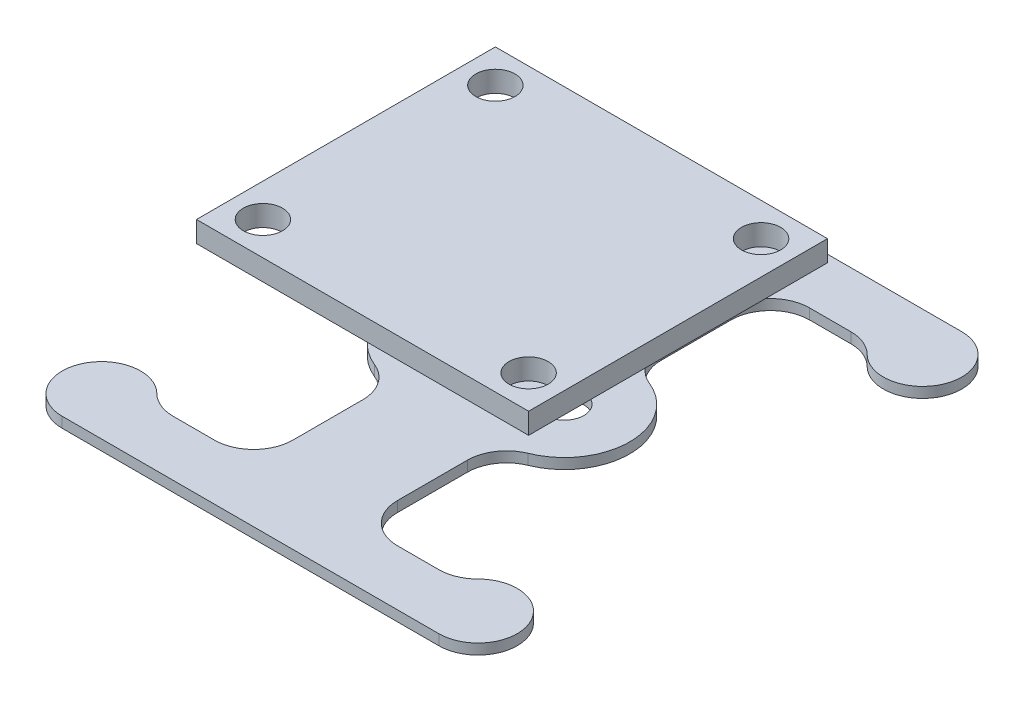
SolidWorks part; units mm, degrees
other "PCB" parameters "D1"=2.5369, "D2"=3.8414, "D7"=2.4726, "D8"=4.6276, "D9"=2.9996, "D3"=14.7024, "D4"=7.7197, "D5"=9.1404, "D6"=29.1565, "D10"=2.8284
ref_plane "Front Plane" through (0, 0, 0) normal (0, 0, 1) x (1, 0, 0)
ref_plane "Top Plane" through (0, 0, 0) normal (0, 1, 0) x (1, 0, 0)
ref_plane "Right Plane" through (0, 0, 0) normal (1, 0, 0) x (0, 0, -1)
sketch "Sketch1" plane through (0, 0, 0) normal (0, 1, 0) x (1, 0, 0)
  line L1 (-12.7, -11.43) -> (12.7, -11.43)
  line L2 (-12.7, -11.43) -> (-12.7, 11.43)
  line L3 (-12.7, 11.43) -> (12.7, 11.43)
  line L4 (12.7, -11.43) -> (12.7, 11.43)
  line L5 (0, 11.43) -> (0, -11.43) construction
  line L6 (-12.7, 0) -> (12.7, 0) construction
  line L7 (10.16, -8.89) -> (-10.16, -8.89) construction
  line L8 (10.16, -8.89) -> (10.16, 8.89) construction
  line L9 (10.16, 8.89) -> (-10.16, 8.89) construction
  line L10 (-10.16, -8.89) -> (-10.16, 8.89) construction
  line L11 (0, 8.89) -> (0, -8.89) construction
  line L12 (10.16, 0) -> (-10.16, 0) construction
  circle A0 centre (-10.16, 8.89) radius 1.5
  circle A1 centre (10.16, 8.89) radius 1.5
  circle A2 centre (10.16, -8.89) radius 1.5
  circle A3 centre (-10.16, -8.89) radius 1.5
  point P0 (0, 0)
  point P4 (0, 0)
  point P12 (0, 0)
  point P13 (0, 0)
  point P14 (0, 0)
  point P15 (0, 0)
  point P16 (0, 0)
  dimension "D5" = 3
  dimension "D1" = 22.86
  dimension "D2" = 25.4
  dimension "D3" = 17.78
  dimension "D4" = 20.32
extrude "Boss-Extrude1" add sketch "Sketch1" along normal blind 1.6
sketch "Sketch2" [suppressed] plane through (0, 0, 0) normal (0, -1, 0) x (1, 0, 0)
  line L0 (-12.7, 11.43) -> (12.7, 11.43) construction
  line L1 (-12.7, -11.43) -> (12.7, -11.43) construction
  line L4 (12.7, 11.43) -> (12.7, -11.43) construction
  line L5 (13.7441, -5.6224) -> (12.8573, -6.4309) construction
  line L6 (6.8924, 12.4741) -> (7.7009, 11.5873) construction
  circle A0 centre (-10.16, 8.89) radius 1.25
  circle A1 centre (-10.16, -8.89) radius 1.25
  circle A2 centre (10.16, -8.89) radius 1.25
  circle A3 centre (10.16, 8.89) radius 1.25
  circle A4 centre (-10.16, 8.89) radius 3.65
  circle A5 centre (-10.16, -8.89) radius 3.65
  circle A6 centre (10.16, -8.89) radius 3.65
  circle A7 centre (10.16, 8.89) radius 3.65
  circle A8 centre (4.1975, 15.43) radius 4
  circle A9 centre (4.1975, 15.43) radius 1.8
  circle A12 centre (16.7, -2.9275) radius 4
  circle A13 centre (16.7, -2.9275) radius 1.8
  circle A16 centre (-4.1975, -15.43) radius 1.8
  circle A17 centre (-4.1975, -15.43) radius 4
  circle A18 centre (-16.7, 2.9275) radius 4
  circle A19 centre (-16.7, 2.9275) radius 1.8
  point P25 (17.3377, -1.52)
  point P28 (-3.6878, -23.8739)
  point P29 (0, 0)
  point P33 (1.6609, -15.6434)
  point P36 (-3.0642, -15.43)
  point P43 (-3.5498, -5.6007)
  point P52 (0, 0)
  dimension "D1" = 2.5
  dimension "D3" = 8
  dimension "D4" = 3.6
  dimension "D5" = 1.2
  dimension "D2" = 2.4
  dimension "D6" = 2
extrude "Boss-Extrude2" [suppressed] add sketch "Sketch2" along normal blind 10 separate body
sketch "Sketch3" [suppressed] plane through (0, -10, 0) normal (0, -1, 0) x (1, 0, 0)
  line L0 (-10.16, 12.54) -> (-10.16, 13.74) construction
  line L1 (-20.7, -19.43) -> (20.7, -19.43)
  line L2 (-20.7, -19.43) -> (-20.7, 19.43)
  line L3 (-20.7, 19.43) -> (20.7, 19.43)
  line L4 (20.7, -19.43) -> (20.7, 19.43)
  line L5 (0, 19.43) -> (0, -19.43) construction
  line L6 (-20.7, 0) -> (20.7, 0) construction
  line L7 (15.01, -13.74) -> (-15.01, -13.74)
  line L8 (15.01, -13.74) -> (15.01, 13.74)
  line L9 (15.01, 13.74) -> (-15.01, 13.74)
  line L10 (-15.01, -13.74) -> (-15.01, 13.74)
  line L11 (0, 13.74) -> (0, -13.74) construction
  line L12 (15.01, 0) -> (-15.01, 0) construction
  line L13 (-13.81, 8.89) -> (-15.01, 8.89) construction
  circle A0 centre (4.1975, 15.43) radius 4 construction
  circle A1 centre (-16.7, 2.9275) radius 4 construction
  circle A2 centre (-10.16, 8.89) radius 3.65 construction
  point P0 (0, 0)
  point P8 (0, 0)
  point P12 (-10.16, 12.54)
  point P13 (-13.81, 8.89)
  point P20 (-16.2622, 15.2267)
  dimension "D1" = 1.2
extrude "Boss-Extrude3" [suppressed] add sketch "Sketch3" against normal up to surface (10 mm away)
sketch "Sketch4" [suppressed] plane through (0, 0, 0) normal (0, 1, 0) x (1, 0, 0)
  circle A0 centre (-16.7, -2.9275) radius 1.8 construction
  circle A1 centre (-4.1975, 15.43) radius 1.8 construction
  circle A2 centre (16.7, 2.9275) radius 1.8 construction
  circle A3 centre (4.1975, -15.43) radius 1.8 construction
  circle A4 centre (-16.7, -2.9275) radius 1.8
  circle A5 centre (-4.1975, 15.43) radius 1.8
  circle A6 centre (16.7, 2.9275) radius 1.8
  circle A7 centre (4.1975, -15.43) radius 1.8
extrude "Cut-Extrude1" [suppressed] cut sketch "Sketch4" against normal through all
chamfer "Chamfer1" [suppressed] distance 2 angle 45
ref_plane "Plane1" [suppressed] through (0, -2, 0) normal (0, 1, 0) x (1, 0, 0)
ref_plane "Plane2" [suppressed] through (0, -8, 0) normal (0, -1, 0) x (-1, 0, 0)
sketch "Sketch5" [suppressed] plane through (0, -2, 0) normal (0, 1, 0) x (1, 0, 0)
  line L0 (-5.0829, 11.5292) -> (6.51, 8.8981)
  line L3 (-5.0829, 11.5292) -> (-4.7287, 13.0895)
  line L4 (6.51, 8.8981) -> (6.8641, 10.4584)
  line L5 (-4.7287, 13.0895) -> (6.8641, 10.4584)
  line L6 (6.6871, 9.6782) -> (-4.9058, 12.3094) construction
  line L7 (0.7136, 10.2136) -> (1.0677, 11.774) construction
  line L9 (12.841, 3.9801) -> (10.3253, -5.2437)
  line L10 (12.841, 3.9801) -> (14.3846, 3.5591)
  line L11 (10.3253, -5.2437) -> (11.8689, -5.6647)
  line L12 (14.3846, 3.5591) -> (11.8689, -5.6647)
  line L13 (11.0971, -5.4542) -> (13.6128, 3.7696) construction
  line L14 (11.5831, -0.6318) -> (13.1267, -1.0528) construction
  line L15 (5.0829, -11.5292) -> (-6.51, -8.8981)
  line L16 (5.0829, -11.5292) -> (4.7287, -13.0895)
  line L17 (4.7287, -13.0895) -> (-6.8641, -10.4584)
  line L18 (-6.51, -8.8981) -> (-6.8641, -10.4584)
  line L19 (-12.841, -3.9801) -> (-10.3253, 5.2437)
  line L20 (-12.841, -3.9801) -> (-14.3846, -3.5591)
  line L21 (-14.3846, -3.5591) -> (-11.8689, 5.6647)
  line L22 (-10.3253, 5.2437) -> (-11.8689, 5.6647)
  circle A2 centre (-4.1975, 15.43) radius 4 construction
  circle A3 centre (10.16, 8.89) radius 3.65 construction
  circle A4 centre (10.16, -8.89) radius 3.65 construction
  circle A5 centre (16.7, 2.9275) radius 4 construction
  circle A6 centre (-16.7, -2.9275) radius 4 construction
  point P1 (0.8906, 10.9938)
  point P7 (-1.7515, -2.2398)
  point P10 (12.3549, -0.8423)
  point P17 (-11.2389, 3.2685)
  point P18 (0, 0)
  point P25 (0, 0)
  dimension "D1" = 1.6
  dimension "D2" = 2
extrude "Boss-Extrude4" [suppressed] add sketch "Sketch5" against normal up to surface (6 mm away)
fillet "Fillet2" [suppressed] radius 1.6
sketch "Sketch6" [suppressed] plane through (0, -10, 0) normal (0, -1, 0) x (1, 0, 0)
  circle A0 centre (10.16, -8.89) radius 3.65 construction
  circle A1 centre (10.16, 8.89) radius 3.65 construction
  circle A2 centre (-10.16, 8.89) radius 3.65 construction
  circle A3 centre (-10.16, -8.89) radius 3.65 construction
  circle A4 centre (10.16, -8.89) radius 3.65
  circle A5 centre (10.16, 8.89) radius 3.65
  circle A6 centre (-10.16, 8.89) radius 3.65
  circle A7 centre (-10.16, -8.89) radius 3.65
extrude "Cut-Extrude2" [suppressed] cut sketch "Sketch6" against normal up to surface (2 mm away)
fillet "Fillet3" [suppressed] radius 2
fillet "Fillet1" [suppressed] radius 6
ref_plane "Plane3" through (0, -8, 0) normal (0, -1, 0) x (-1, 0, 0)
sketch "Sketch7" [suppressed] plane through (0, 0, 0) normal (0, 0, 1) x (1, 0, 0)
  line L0 (-5.16, 0) -> (-15.16, 0)
  line L1 (-15.16, -8) -> (0, -8)
  line L2 (-12.573, -8) -> (12.573, -8) construction
  arc A0 (-15.16, 0) -> (-15.16, -8) centre (-15.16, -4) ccw
  point P4 (-10.16, 0)
  point P10 (0, 0)
  dimension "D1" = 5
sketch "Sketch8" [suppressed] plane through (0, -8, 0) normal (0, -1, 0) x (-1, 0, 0)
  line L0 (-6, 0) -> (6, 0) construction
  line L1 (5.5791, 6) -> (-5.5791, 6)
  line L2 (5.5791, 6) -> (13.4691, 13.89)
  line L3 (13.4691, 13.89) -> (32.7264, 13.89)
  line L5 (-10.16, 8.89) -> (10.16, 8.89) construction
  line L6 (0, 11.43) -> (0, -11.43) construction
  line L8 (24.9804, 9.89) -> (17.3363, 9.89)
  line L9 (12, -4.5537) -> (12, 4.5537)
  line L10 (-1000, 0) -> (49000, 0) construction
  line L11 (0, -1000) -> (0, 49000) construction
  line L14 (-13.4691, 13.89) -> (-32.7264, 13.89)
  line L15 (-5.5791, 6) -> (-13.4691, 13.89)
  line L20 (-13.4691, -13.89) -> (-32.7264, -13.89)
  line L21 (-5.5791, -6) -> (-13.4691, -13.89)
  line L22 (5.5791, -6) -> (-5.5791, -6)
  line L23 (5.5791, -6) -> (13.4691, -13.89)
  line L24 (13.4691, -13.89) -> (32.7264, -13.89)
  line L27 (13.563, 8.327) -> (10.7345, 11.1555) construction
  line L28 (21.1583, 9.89) -> (21.1583, 13.89) construction
  line L29 (24.9804, -9.89) -> (17.3363, -9.89)
  line L30 (-24.9804, 9.89) -> (-17.3363, 9.89)
  line L31 (-12, -4.5537) -> (-12, 4.5537)
  line L32 (-24.9804, -9.89) -> (-17.3363, -9.89)
  circle A0 centre (32.7264, 8.89) radius 1.4
  circle A1 centre (-6, 0) radius 1.7
  circle A2 centre (6, 0) radius 1.7
  arc A3 (32.7264, 13.89) -> (27.8851, 7.64) centre (32.7264, 8.89) cw
  arc A4 (27.8851, 7.64) -> (24.9804, 9.89) centre (24.9804, 6.89) ccw
  circle A5 centre (-32.7264, 8.89) radius 1.4
  arc A6 (-32.7264, 13.89) -> (-27.8851, 7.64) centre (-32.7264, 8.89) ccw
  circle A7 centre (32.7264, -8.89) radius 1.4
  arc A8 (32.7264, -13.89) -> (27.8851, -7.64) centre (32.7264, -8.89) ccw
  circle A9 centre (-32.7264, -8.89) radius 1.4
  arc A10 (-32.7264, -13.89) -> (-27.8851, -7.64) centre (-32.7264, -8.89) cw
  circle A15 centre (6, 0) radius 6 construction
  arc A16 (17.3363, 9.89) -> (12, 4.5537) centre (17.3363, 4.5537) ccw
  arc A17 (17.3363, -9.89) -> (12, -4.5537) centre (17.3363, -4.5537) cw
  arc A18 (27.8851, -7.64) -> (24.9804, -9.89) centre (24.9804, -6.89) cw
  arc A19 (-27.8851, 7.64) -> (-24.9804, 9.89) centre (-24.9804, 6.89) cw
  arc A20 (-17.3363, 9.89) -> (-12, 4.5537) centre (-17.3363, 4.5537) cw
  arc A21 (-17.3363, -9.89) -> (-12, -4.5537) centre (-17.3363, -4.5537) ccw
  arc A22 (-27.8851, -7.64) -> (-24.9804, -9.89) centre (-24.9804, -6.89) ccw
  point P6 (0, 0)
  point P20 (37.7264, 8.89)
  point P38 (0, 6)
  point P43 (13.4691, 7.2737)
  point P44 (12, 4.7495)
  point P45 (12, 5.3195)
  point P55 (12, 0)
  dimension "D1" = 2.8
  dimension "D2" = 3.4
  dimension "D8" = 5
  dimension "D9" = 3
  dimension "D3" = 12
  dimension "D4" = 45
  dimension "D6" = 37.7264
  dimension "D7" = 6
  dimension "D5" = 4
extrude "Boss-Extrude5" [suppressed] add sketch "Sketch8" along normal blind 0.8 separate body
fillet "Fillet4" [suppressed] radius 6
sketch "Sketch9" [suppressed] plane through (0, -8, 0) normal (0, 1, 0) x (1, 0, 0)
  circle A0 centre (32.7264, 8.89) radius 1.4 construction
  circle A1 centre (32.7264, -8.89) radius 1.4 construction
  circle A2 centre (-32.7264, -8.89) radius 1.4 construction
  circle A3 centre (-32.7264, 8.89) radius 1.4 construction
  circle A4 centre (32.7264, 8.89) radius 1.4
  circle A5 centre (32.7264, -8.89) radius 1.4
  circle A6 centre (-32.7264, -8.89) radius 1.4
  circle A7 centre (-32.7264, 8.89) radius 1.4
  circle A8 centre (-32.7264, 8.89) radius 5
  circle A9 centre (-32.7264, -8.89) radius 5
  circle A10 centre (32.7264, -8.89) radius 5
  circle A11 centre (32.7264, 8.89) radius 5
extrude "Boss-Extrude6" [suppressed] add sketch "Sketch9" along normal blind 3
sketch "Sketch10" plane through (0, -8, 0) normal (0, -1, 0) x (-1, 0, 0)
  line L0 (-4, 0) -> (4, 0) construction
  line L1 (-4, 7.4162) -> (-4, 12.7574)
  line L2 (-7, 15.7574) -> (-10.16, 15.7574)
  line L3 (-10.16, -8.89) -> (-10.16, 8.89) construction
  line L4 (0, -1000) -> (0, 49000) construction
  line L5 (-12.2813, 14.8787) -> (-11.4026, 15.7574) construction
  line L6 (-11.4026, 15.7574) -> (-10.16, 15.7574) construction
  line L8 (7, 15.7574) -> (10.16, 15.7574)
  line L9 (4, 7.4162) -> (4, 12.7574)
  line L10 (7, -15.7574) -> (10.16, -15.7574)
  line L11 (4, -7.4162) -> (4, -12.7574)
  line L12 (-4, -7.4162) -> (-4, -12.7574)
  line L13 (-7, -15.7574) -> (-10.16, -15.7574)
  line L14 (-14.4026, 20) -> (14.4026, 20)
  line L15 (14.4026, -20) -> (-14.4026, -20)
  circle A0 centre (-4, 0) radius 1.5
  circle A1 centre (4, 0) radius 1.5
  arc A2 (-5.875, 4.6351) -> (-5.875, -4.6351) centre (-4, 0) ccw
  arc A3 (-5.875, 4.6351) -> (-4, 7.4162) centre (-7, 7.4162) ccw
  arc A4 (-4, 12.7574) -> (-7, 15.7574) centre (-7, 12.7574) ccw
  arc A5 (-10.16, 15.7574) -> (-12.2813, 14.8787) centre (-10.16, 12.7574) ccw
  arc A6 (-12.2813, 14.8787) -> (-14.4026, 20) centre (-14.4026, 17) cw
  arc A7 (12.2813, 14.8787) -> (14.4026, 20) centre (14.4026, 17) ccw
  arc A8 (10.16, 15.7574) -> (12.2813, 14.8787) centre (10.16, 12.7574) cw
  arc A9 (4, 12.7574) -> (7, 15.7574) centre (7, 12.7574) cw
  arc A10 (5.875, 4.6351) -> (4, 7.4162) centre (7, 7.4162) cw
  arc A11 (5.875, 4.6351) -> (5.875, -4.6351) centre (4, 0) cw
  arc A12 (12.2813, -14.8787) -> (14.4026, -20) centre (14.4026, -17) cw
  arc A13 (10.16, -15.7574) -> (12.2813, -14.8787) centre (10.16, -12.7574) ccw
  arc A14 (4, -12.7574) -> (7, -15.7574) centre (7, -12.7574) ccw
  arc A15 (5.875, -4.6351) -> (4, -7.4162) centre (7, -7.4162) ccw
  arc A16 (-5.875, -4.6351) -> (-4, -7.4162) centre (-7, -7.4162) cw
  arc A17 (-4, -12.7574) -> (-7, -15.7574) centre (-7, -12.7574) cw
  arc A18 (-10.16, -15.7574) -> (-12.2813, -14.8787) centre (-10.16, -12.7574) cw
  arc A19 (-12.2813, -14.8787) -> (-14.4026, -20) centre (-14.4026, -17) ccw
  point P4 (0, 0)
  point P36 (-9, 0)
  point P57 (-4.4829, -13.1786)
  dimension "D1" = 3
  dimension "D3" = 5
  dimension "D4" = 3
  dimension "D5" = 3
  dimension "D2" = 8
  dimension "D6" = 45
  dimension "D7" = 8
  dimension "D8" = 20
extrude "Boss-Extrude7" add sketch "Sketch10" along normal blind 0.8 separate body
equation "\"D6@Sketch8\"=\"D2@Sketch7\""
equation "\"D8@Sketch8\"=\"D1@Sketch7\""
